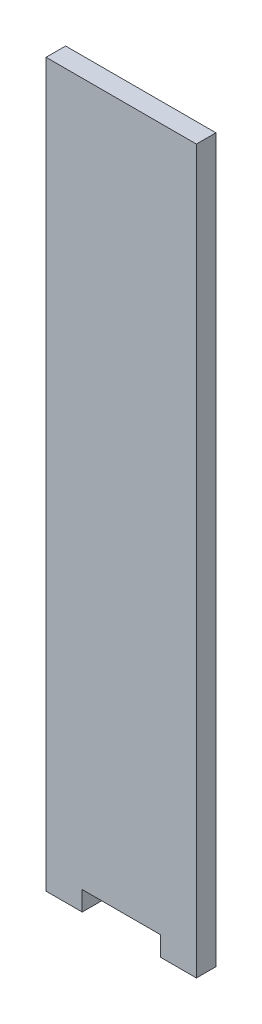
SolidWorks part; units mm, degrees
ref_plane "Front Plane" through (0, 0, 0) normal (0, 0, 1) x (1, 0, 0)
ref_plane "Top Plane" through (0, 0, 0) normal (0, 1, 0) x (1, 0, 0)
ref_plane "Right Plane" through (0, 0, 0) normal (1, 0, 0) x (0, 0, -1)
sketch "Sketch1" plane through (0, 0, 0) normal (0, 0, 1) x (1, 0, 0)
  line L0 (0, 0) -> (0, 76.8217) construction
  line L1 (-19.25, 180) -> (19.25, 180)
  line L2 (-19.25, 180) -> (-19.25, 0)
  line L3 (-10, 0) -> (10, 0)
  line L4 (19.25, 180) -> (19.25, 0)
  line L6 (-19.25, -5) -> (-10, -5)
  line L8 (-10, -5) -> (-10, 0)
  line L9 (-19.25, -5) -> (-19.25, 0)
  line L10 (19.25, 0) -> (19.25, -5)
  line L11 (19.25, -5) -> (10, -5)
  line L12 (10, -5) -> (10, 0)
  line L14 (-19.25, 0) -> (-10, 0) construction
  line L15 (10, 0) -> (19.25, 0) construction
  dimension "D1" = 38.5
  dimension "D2" = 180
  dimension "D3" = 5
  dimension "D4" = 9.25
  dimension "D5" = 20
extrude "Boss-Extrude1" add sketch "Sketch1" along normal blind 5
